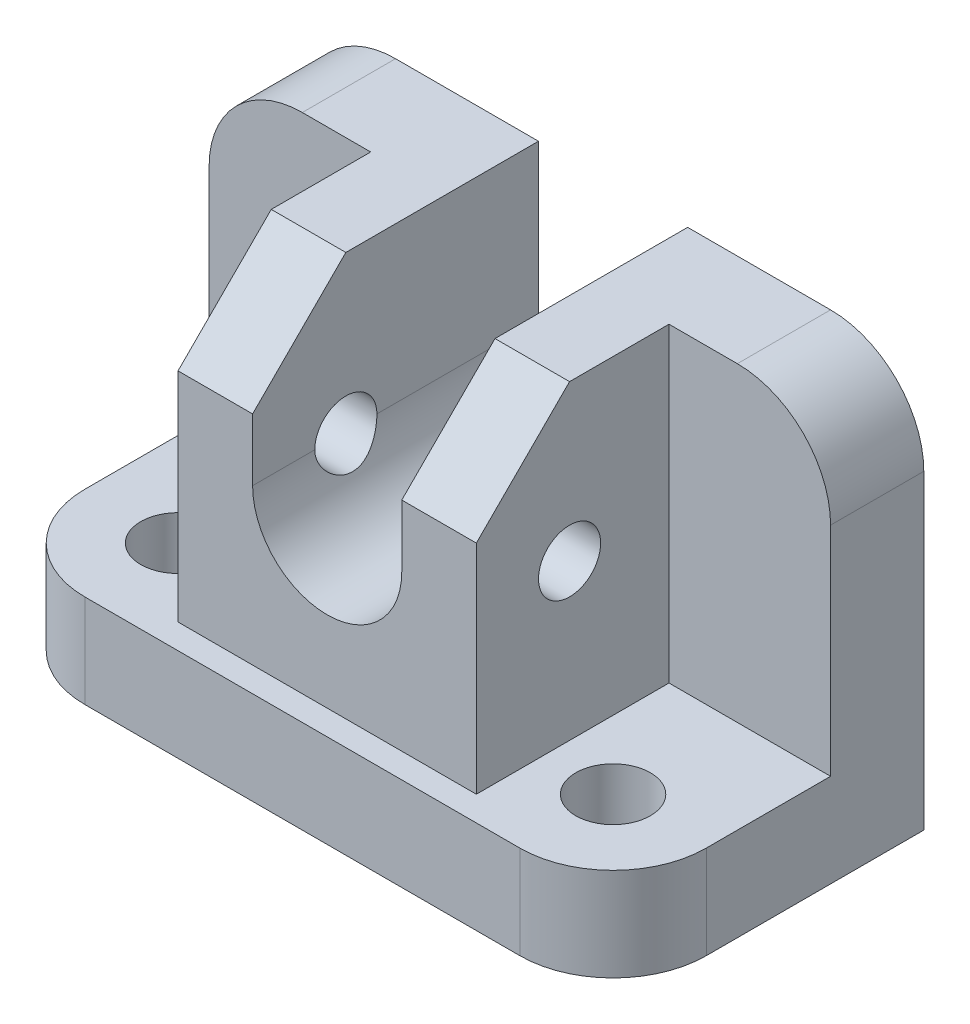
SolidWorks part; units mm, degrees
ref_plane "Front Plane" through (0, 0, 0) normal (0, 0, 1) x (1, 0, 0)
ref_plane "Top Plane" through (0, 0, 0) normal (0, 1, 0) x (1, 0, 0)
ref_plane "Right Plane" through (0, 0, 0) normal (1, 0, 0) x (0, 0, -1)
sketch "Sketch1" plane through (0, 0, 0) normal (0, 1, 0) x (1, 0, 0)
  line L0 (-50, 0) -> (50, 0)
  line L1 (50, 0) -> (50, -50)
  line L2 (50, -50) -> (-50, -50)
  line L3 (-50, -50) -> (-50, 0)
  point P3 (0, 0)
  dimension "D1" = 50
  dimension "D2" = 100
extrude "Boss-Extrude1" add sketch "Sketch1" along normal blind 15
sketch "Sketch2" plane through (0, 0, 0) normal (0, 0, 1) x (1, 0, 0)
  line L0 (-50, 0) -> (-50, 65)
  line L1 (-50, 65) -> (50, 65)
  line L2 (50, 65) -> (50, 0)
  line L3 (-50, 0) -> (50, 0)
  dimension "D1" = 65
extrude "Boss-Extrude2" add sketch "Sketch2" along normal blind 46
sketch "Sketch3" plane through (0, 0, 46) normal (0, 0, 1) x (1, 0, 0)
  line L0 (0, 71.0882) -> (0, -4.7947) construction
  line L1 (-12, 65) -> (-12, 40)
  line L2 (50, 65) -> (-50, 65) construction
  line L3 (-12, 65) -> (12, 65)
  line L4 (12, 65) -> (12, 40)
  arc A0 (-12, 40) -> (0, 28) centre (0, 40) ccw
  arc A1 (12, 40) -> (0, 28) centre (0, 40) cw
  point P13 (0, 65)
  dimension "D1" = 12
  dimension "D2" = 25
extrude "Cut-Extrude1" cut sketch "Sketch3" against normal through all
sketch "Sketch4" plane through (-12, 0, 0) normal (1, 0, 0) x (0, 0, -1)
  line L0 (-31, 65) -> (-46, 50)
  line L1 (0, 65) -> (-46, 65) construction
  line L2 (-46, 65) -> (-46, 40) construction
  line L3 (-46, 50) -> (-46, 65)
  line L4 (-46, 65) -> (-31, 65)
  dimension "D1" = 15
  dimension "D2" = 15
extrude "Cut-Extrude2" cut sketch "Sketch4" against normal through all
mirror "Mirror1" about plane through (0, 0, 0) normal (1, 0, 0) of "Cut-Extrude2"
sketch "Sketch5" plane through (-50, 0, 0) normal (-1, 0, 0) x (0, 0, 1)
  line L0 (15, 65) -> (15, 15)
  line L1 (31, 65) -> (0, 65) construction
  line L2 (15, 15) -> (46, 15)
  line L3 (46, 15) -> (46, 50)
  line L4 (46, 50) -> (31, 65)
  line L5 (31, 65) -> (15, 65)
  line L6 (0, 65) -> (0, 0) construction
  dimension "D1" = 15
extrude "Cut-Extrude3" cut sketch "Sketch5" against normal blind 26
mirror "Mirror2" about plane through (0, 0, 0) normal (1, 0, 0) of "Cut-Extrude3"
fillet "Fillet1" radius 15 4 edges at (50, 7.5, 50) (50, 65, 7.5) (-50, 7.5, 50) (-50, 65, 7.5)
sketch "Sketch6" plane through (24, 0, 0) normal (1, 0, 0) x (0, 0, -1)
  line L0 (-46, 15) -> (-46, 50) construction
  line L1 (-31, 65) -> (-15, 65) construction
  circle A0 centre (-31, 40) radius 5
  dimension "D1" = 10
  dimension "D2" = 15
  dimension "D3" = 25
extrude "Cut-Extrude4" cut sketch "Sketch6" against normal through all
sketch "Sketch7" plane through (0, 15, 0) normal (0, 1, 0) x (1, 0, 0)
  circle A0 centre (-35, -35) radius 6
  arc A1 (-50, -35) -> (-35, -50) centre (-35, -35) ccw construction
  dimension "D1" = 12
extrude "Cut-Extrude5" cut sketch "Sketch7" against normal blind 26
mirror "Mirror3" about plane through (0, 0, 0) normal (1, 0, 0) of "Cut-Extrude5"
